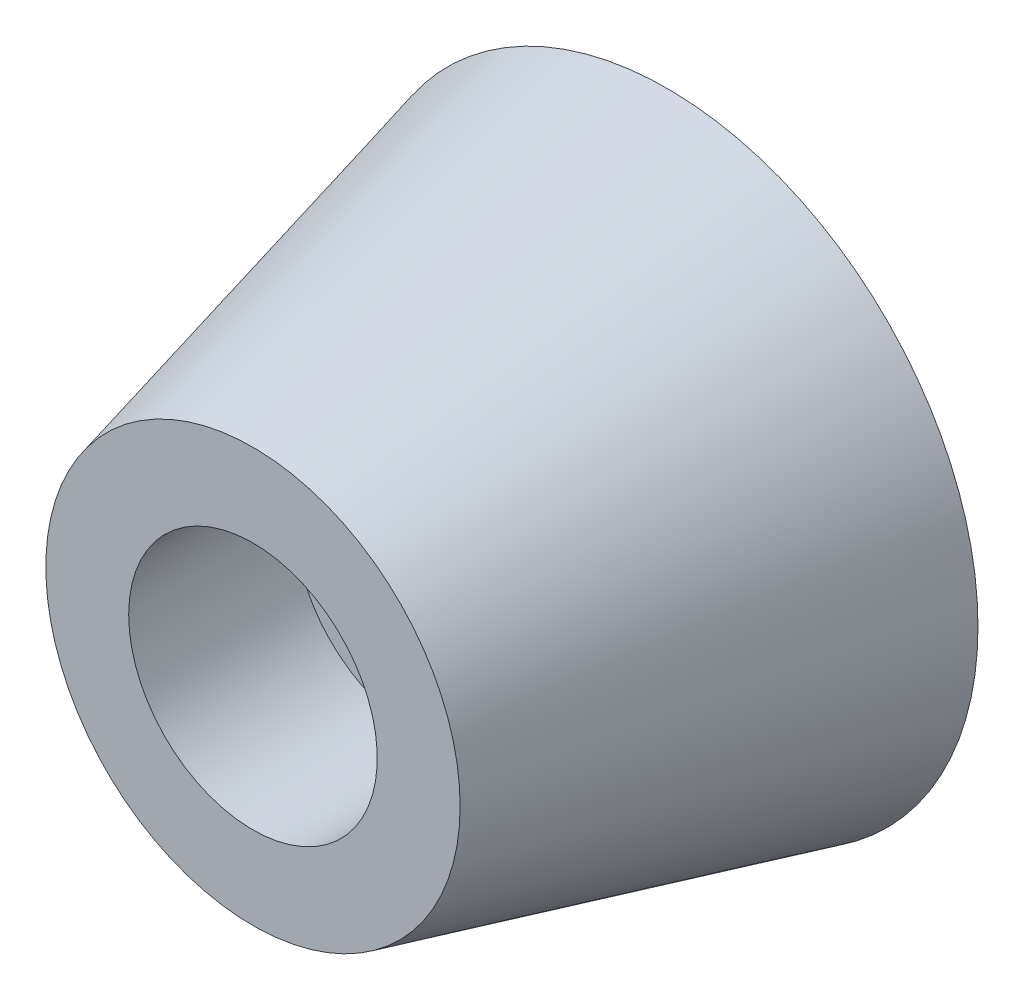
SolidWorks part; units mm, degrees
ref_plane "Front Plane" through (0, 0, 0) normal (0, 0, 1) x (1, 0, 0)
ref_plane "Top Plane" through (0, 0, 0) normal (0, 1, 0) x (1, 0, 0)
ref_plane "Right Plane" through (0, 0, 0) normal (1, 0, 0) x (0, 0, -1)
sketch "Sketch1" plane through (0, 0, 0) normal (0, 0, 1) x (1, 0, 0)
  circle A0 centre (0, 0) radius 7.4986
  dimension "D1" = 14.9971
ref_plane "Plane1" through (0, 0, 10) normal (0, 0, 1) x (1, 0, 0)
sketch "Sketch2" plane through (0, 0, 10) normal (0, 0, 1) x (1, 0, 0)
  circle A1 centre (0, 0) radius 5
  dimension "D1" = 10
loft "Loft1" add profiles "Sketch1", "Sketch2"
sketch "Sketch3" plane through (0, 0, 10) normal (0, 0, -1) x (-1, 0, 0)
  circle A0 centre (0, 0) radius 3
  dimension "D1" = 6
extrude "Cut-Extrude1" cut sketch "Sketch3" along normal blind 4
sketch "Sketch4" plane through (0, 0, 6) normal (0, 0, 1) x (1, 0, 0)
  circle A0 centre (0, 0) radius 1.75
  dimension "D1" = 3.5
extrude "Cut-Extrude2" cut sketch "Sketch4" against normal blind 10
